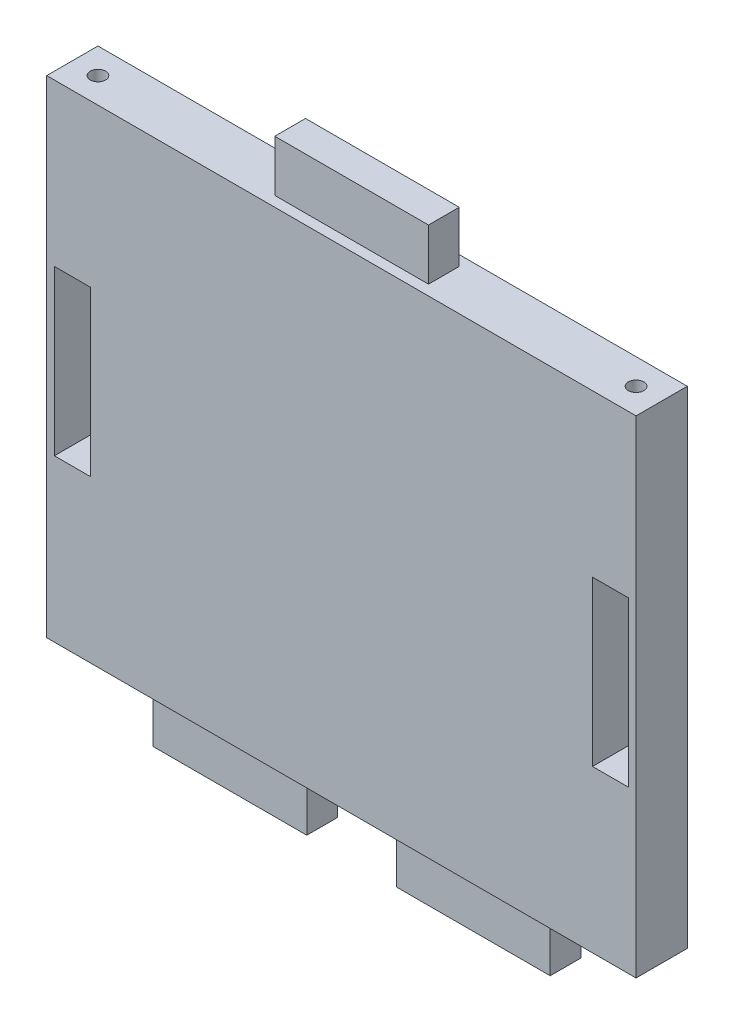
SolidWorks part; units mm, degrees
ref_plane "Plano frontal" through (0, 0, 0) normal (0, 0, 1) x (1, 0, 0)
ref_plane "Plano superior" through (0, 0, 0) normal (0, 1, 0) x (1, 0, 0)
ref_plane "Plano direito" through (0, 0, 0) normal (1, 0, 0) x (0, 0, -1)
sketch "Esboço1" plane through (0, 0, 0) normal (0, 0, 1) x (1, 0, 0)
  line L1 (57.5, -47.5) -> (-57.5, -47.5)
  line L2 (57.5, -47.5) -> (57.5, 47.5)
  line L3 (57.5, 47.5) -> (-57.5, 47.5)
  line L4 (-57.5, -47.5) -> (-57.5, 47.5)
  line L5 (57.5, -47.5) -> (-57.5, 47.5) construction
  line L6 (57.5, 47.5) -> (-57.5, -47.5) construction
  point P0 (0, 0)
  dimension "D1" = 95
  dimension "D2" = 115
extrude "Ressalto-extrusão1" add sketch "Esboço1" along normal blind 10
sketch "Esboço2" plane through (0, 47.5, 0) normal (0, 1, 0) x (1, 0, 0)
  line L0 (57.5, -5) -> (-57.5, -5) construction
  line L1 (57.5, -10) -> (57.5, 0) construction
  line L2 (-57.5, -10) -> (-57.5, 0) construction
  line L3 (0, 0) -> (0, -10) construction
  line L4 (57.5, -10) -> (-57.5, -10) construction
  line L6 (15, -8) -> (-15, -8)
  line L7 (15, -8) -> (15, -2)
  line L8 (15, -2) -> (-15, -2)
  line L9 (-15, -8) -> (-15, -2)
  line L10 (15, -8) -> (-15, -2) construction
  line L11 (15, -2) -> (-15, -8) construction
  point P11 (0, -5)
  dimension "D1" = 30
  dimension "D2" = 6
extrude "Ressalto-extrusão2" add sketch "Esboço2" along normal blind 10
sketch "Esboço3" plane through (0, -47.5, 0) normal (0, -1, 0) x (1, 0, 0)
  line L0 (-57.5, 5) -> (57.5, 5) construction
  line L1 (-57.5, 10) -> (-57.5, 0) construction
  line L2 (57.5, 10) -> (57.5, 0) construction
  line L3 (0, 0) -> (0, 10) construction
  line L4 (-57.5, 0) -> (57.5, 0) construction
  line L5 (-57.5, 10) -> (57.5, 10) construction
  line L6 (8.75, 2) -> (8.75, 8)
  line L7 (-8.75, 2) -> (-38.75, 2)
  line L8 (-8.75, 2) -> (-8.75, 8)
  line L9 (-8.75, 8) -> (-38.75, 8)
  line L10 (-38.75, 2) -> (-38.75, 8)
  line L11 (-8.75, 2) -> (-38.75, 8) construction
  line L12 (-8.75, 8) -> (-38.75, 2) construction
  line L13 (8.75, 2) -> (38.75, 2)
  line L14 (38.75, 2) -> (38.75, 8)
  line L15 (8.75, 8) -> (38.75, 8)
  point P12 (-23.75, 5)
  dimension "D1" = 30
  dimension "D2" = 6
  dimension "D3" = 33.75
extrude "Ressalto-extrusão3" add sketch "Esboço3" along normal blind 10
sketch "Esboço4" plane through (0, 0, 10) normal (0, 0, 1) x (1, 0, 0)
  line L0 (-74.388, 0) -> (91.2943, 0) construction
  line L1 (0, -47.5) -> (0, 47.5) construction
  line L2 (-57.5, -47.5) -> (57.5, -47.5) construction
  line L3 (57.5, 47.5) -> (-57.5, 47.5) construction
  line L4 (-57.5, 47.5) -> (-57.5, -47.5) construction
  line L5 (-49, -16) -> (-56, -16)
  line L6 (-49, -16) -> (-49, 16)
  line L7 (-49, 16) -> (-56, 16)
  line L8 (-56, -16) -> (-56, 16)
  line L9 (-49, -16) -> (-56, 16) construction
  line L10 (-49, 16) -> (-56, -16) construction
  line L11 (49, -16) -> (56, -16)
  line L12 (49, -16) -> (49, 16)
  line L13 (49, 16) -> (56, 16)
  line L14 (56, -16) -> (56, 16)
  point P9 (-52.5, 0)
  dimension "D1" = 32
  dimension "D2" = 7
  dimension "D3" = 1.5
extrude "Corte-extrusão1" cut sketch "Esboço4" against normal through all
sketch "Esboço5" plane through (0, 47.5, 0) normal (0, 1, 0) x (1, 0, 0)
  line L0 (-55.6853, -5) -> (79.0179, -5) construction
  line L1 (57.5, -10) -> (57.5, 0) construction
  line L2 (0, 11.5673) -> (0, -21.2919) construction
  circle A0 centre (52.5, -5) radius 1.5
  circle A1 centre (-52.5, -5) radius 1.5
  dimension "D1" = 3
  dimension "D2" = 5
extrude "Corte-extrusão2" cut sketch "Esboço5" against normal blind 8
sketch "Esboço6" plane through (0, -47.5, 0) normal (0, -1, 0) x (1, 0, 0)
  line L0 (-60.955, 5) -> (58.7599, 5) construction
  line L1 (0, -6.4528) -> (0, 16.6063) construction
  line L2 (-57.5, 10) -> (-57.5, 0) construction
  line L3 (57.5, 10) -> (57.5, 0) construction
  circle A0 centre (-52.5, 5) radius 1.5
  circle A1 centre (52.5, 5) radius 1.5
  dimension "D1" = 3
  dimension "D2" = 5
  dimension "D3" = 3
  dimension "D4" = 5
extrude "Corte-extrusão3" cut sketch "Esboço6" against normal blind 8
